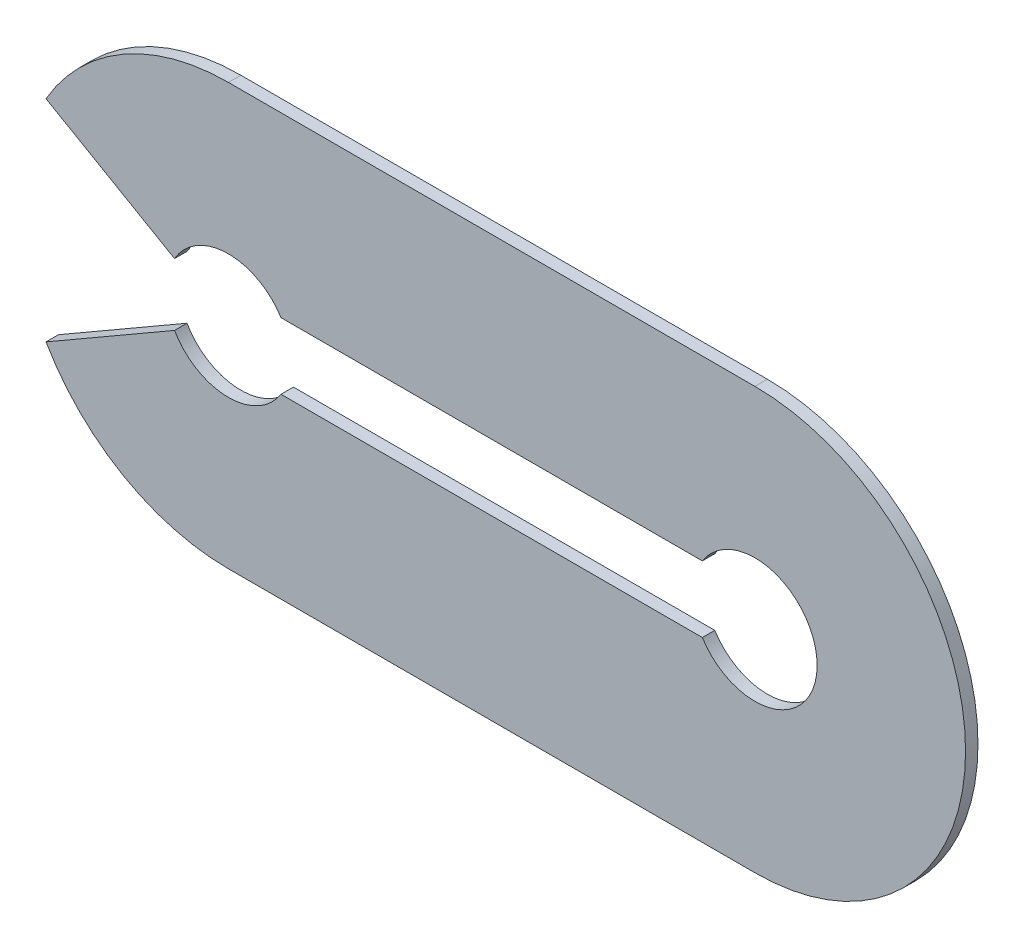
SolidWorks part; units mm, degrees
ref_plane "Plan de face" through (0, 0, 0) normal (0, 0, 1) x (1, 0, 0)
ref_plane "Plan de dessus" through (0, 0, 0) normal (0, 1, 0) x (1, 0, 0)
ref_plane "Plan de droite" through (0, 0, 0) normal (1, 0, 0) x (0, 0, -1)
sketch "Esquisse1" plane through (0, 0, 0) normal (0, 0, 1) x (1, 0, 0)
  line L0 (0, 5.08) -> (-12.7, 5.08)
  line L3 (-1.2689, -0.8) -> (-11.4311, -0.8)
  line L7 (-11.4311, 0.8) -> (-1.2689, 0.8)
  line L9 (0, -5.08) -> (-12.7, -5.08)
  line L10 (-13.999, 0.75) -> (-17.0994, 2.54)
  line L11 (-13.999, -0.75) -> (-17.0994, -2.54)
  arc A0 (0, -5.08) -> (0, 5.08) centre (0, 0) ccw
  arc A1 (-17.0994, -2.54) -> (-12.7, -5.08) centre (-12.7, 0) ccw
  arc A2 (-1.2689, -0.8) -> (-1.2689, 0.8) centre (0, 0) ccw
  arc A3 (-13.999, -0.75) -> (-11.4311, -0.8) centre (-12.7, 0) ccw
  arc A4 (-12.7, 5.08) -> (-17.0994, 2.54) centre (-12.7, 0) ccw
  arc A5 (-11.4311, 0.8) -> (-13.999, 0.75) centre (-12.7, 0) ccw
extrude "Extrusion1" add sketch "Esquisse1" against normal blind 0.3
